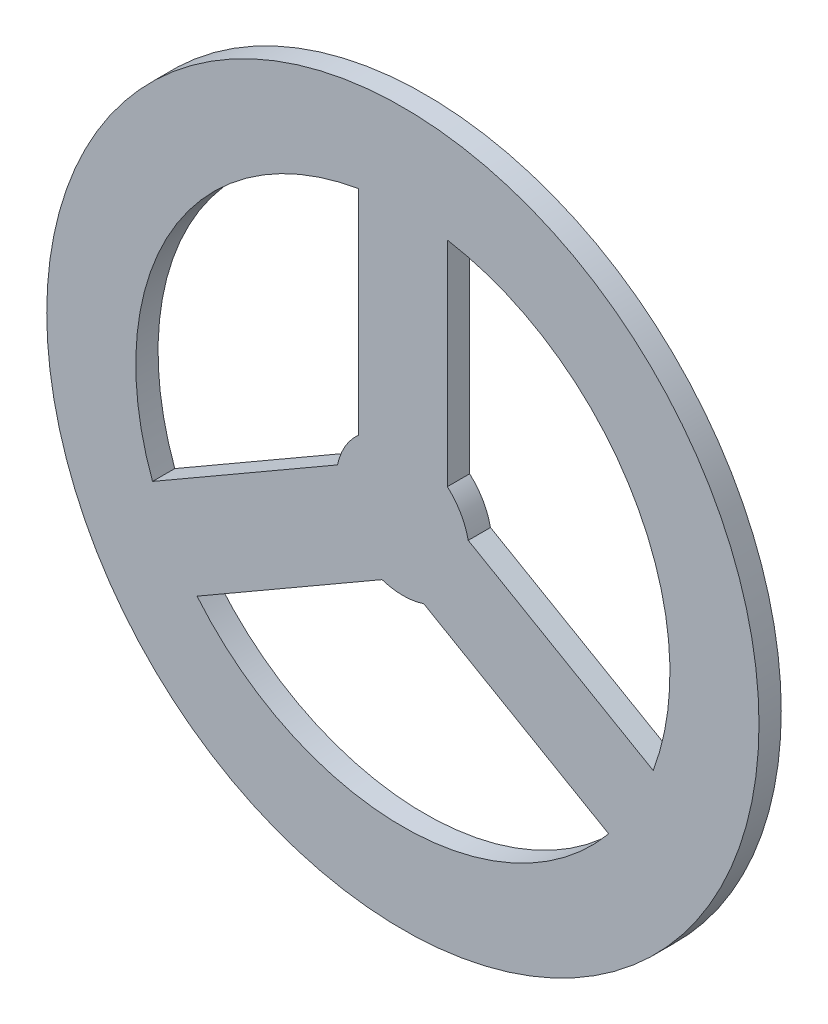
SolidWorks part; units mm, degrees
ref_plane "Front Plane" through (0, 0, 0) normal (0, 0, 1) x (1, 0, 0)
ref_plane "Top Plane" through (0, 0, 0) normal (0, 1, 0) x (1, 0, 0)
ref_plane "Right Plane" through (0, 0, 0) normal (1, 0, 0) x (0, 0, -1)
sketch "Sketch1" plane through (0, 0, 0) normal (0, 0, 1) x (1, 0, 0)
  line L0 (0, 0) -> (0, -134.4882) construction
  line L1 (-12.7, 14.199) -> (-12.7, 75.1342)
  line L2 (12.7, 14.199) -> (12.7, 75.1342)
  line L4 (18.6467, 3.899) -> (71.4181, -26.5686)
  line L5 (5.9467, -18.098) -> (58.7181, -48.5656)
  line L6 (-5.9467, -18.098) -> (-58.7181, -48.5656)
  line L7 (-18.6467, 3.899) -> (-71.4181, -26.5686)
  arc A0 (-12.7, 14.199) -> (-18.6467, 3.899) centre (0, 0) ccw
  circle A1 centre (0, 0) radius 101.6
  arc A2 (-12.7, 75.1342) -> (-71.4181, -26.5686) centre (0, 0) ccw
  arc A3 (-58.7181, -48.5656) -> (58.7181, -48.5656) centre (0, 0) ccw
  arc A4 (-5.9467, -18.098) -> (5.9467, -18.098) centre (0, 0) ccw
  arc A5 (18.6467, 3.899) -> (12.7, 14.199) centre (0, 0) ccw
  arc A6 (71.4181, -26.5686) -> (12.7, 75.1342) centre (0, 0) ccw
  point P21 (0, 0)
  dimension "D1" = 38.1
  dimension "D2" = 203.2
  dimension "D3" = 152.4
  dimension "D4" = 3
extrude "Boss-Extrude1" add sketch "Sketch1" along normal blind 6.35
